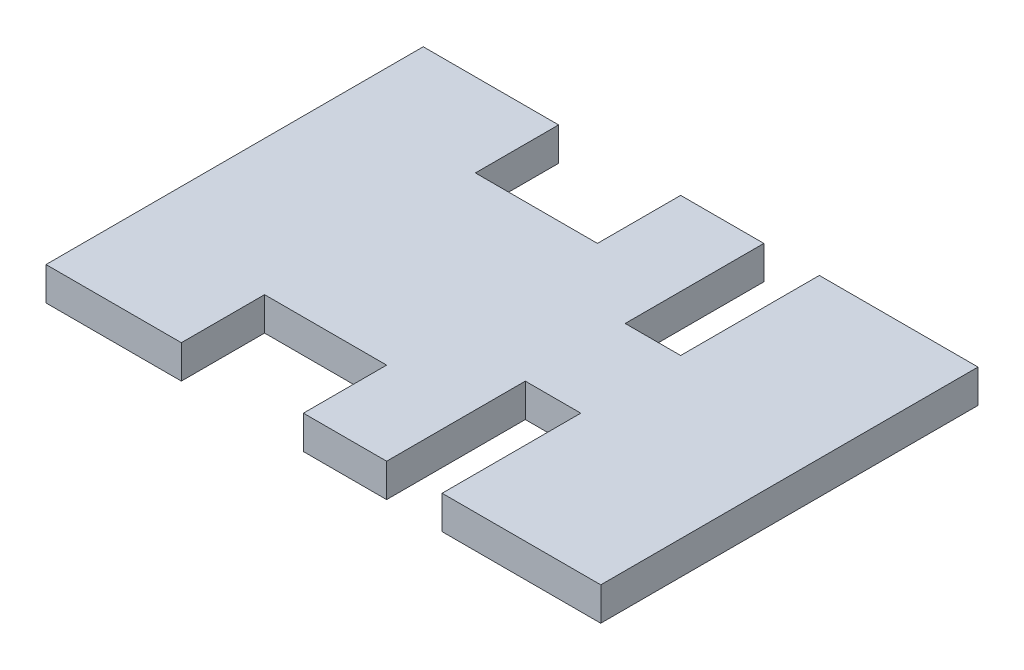
SolidWorks part; units mm, degrees
material "Maple"
ref_plane "Front Plane" through (0, 0, 0) normal (0, 0, 1) x (1, 0, 0)
ref_plane "Top Plane" through (0, 0, 0) normal (0, 1, 0) x (1, 0, 0)
ref_plane "Right Plane" through (0, 0, 0) normal (1, 0, 0) x (0, 0, -1)
sketch "Sketch1" plane through (0, 0, 0) normal (0, 1, 0) x (1, 0, 0)
  line L1 (-50, 34) -> (50, 34)
  line L2 (-50, 34) -> (-50, -34)
  line L3 (-50, -34) -> (50, -34)
  line L4 (50, 34) -> (50, -34)
  line L5 (-50, 34) -> (50, -34) construction
  line L6 (-50, -34) -> (50, 34) construction
  point P0 (0, 0)
  dimension "D1" = 68
  dimension "D2" = 100
extrude "Boss-Extrude1" add sketch "Sketch1" along normal blind 6
ref_plane "Plane1" through (0, 3, 0) normal (0, 1, 0) x (1, 0, 0)
sketch "Sketch2" plane through (0, 6, 0) normal (0, 1, 0) x (1, 0, 0)
  line L1 (16.4, -34) -> (16.4, 97.4) construction
  line L2 (20.4, 97.4) -> (12.4, 97.4) construction
  line L3 (-50, -34) -> (50, -34) construction
  line L4 (-14.6, -34) -> (-14.6, 53.4) construction
  line L5 (-10.6, 53.4) -> (-18.6, 53.4) construction
  line L7 (21.4, -34) -> (11.4, -34)
  line L8 (21.4, -34) -> (21.4, -9)
  line L9 (21.4, -9) -> (11.4, -9)
  line L10 (11.4, -34) -> (11.4, -9)
  line L11 (-3.6, -34) -> (-25.6, -34)
  line L12 (-3.6, -34) -> (-3.6, -19)
  line L13 (-3.6, -19) -> (-25.6, -19)
  line L14 (-25.6, -34) -> (-25.6, -19)
  dimension "D1" = 25
  dimension "D2" = 10
  dimension "D3" = 22
  dimension "D4" = 15
extrude "Cut-Extrude1" cut sketch "Sketch2" against normal through all
mirror "Mirror1" about plane through (0, 0, 0) normal (0, 0, 1) of "Cut-Extrude1"
